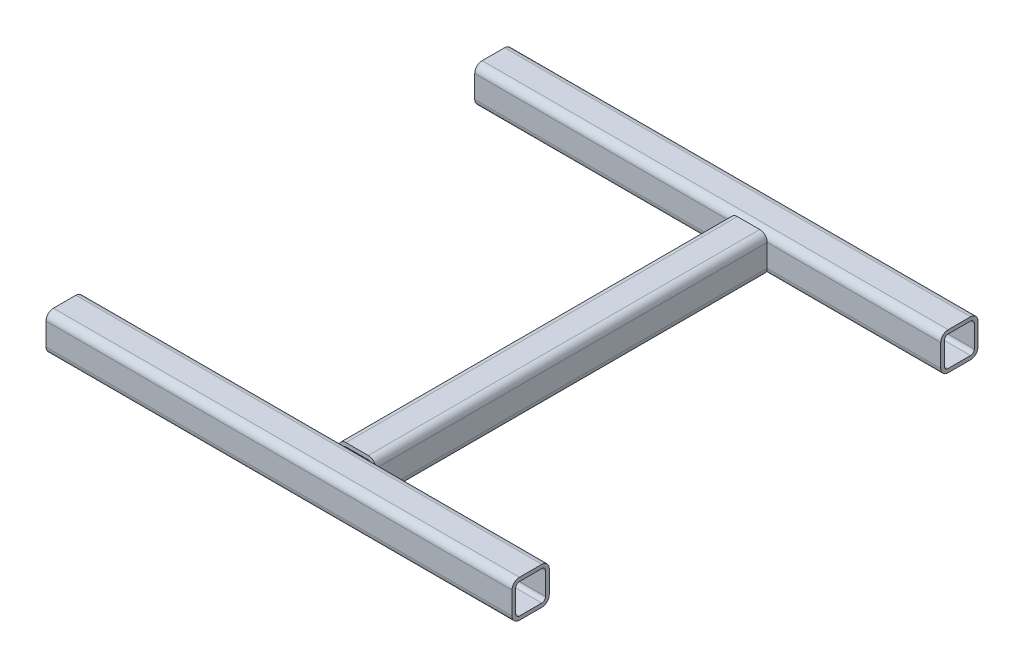
SolidWorks part; units mm, degrees
ref_plane "Front Plane" through (0, 0, 0) normal (0, 0, 1) x (1, 0, 0)
ref_plane "Top Plane" through (0, 0, 0) normal (0, 1, 0) x (1, 0, 0)
ref_plane "Right Plane" through (0, 0, 0) normal (1, 0, 0) x (0, 0, -1)
sketch3d "3DSketch2"
  line L0 (293.8199, 0, 460) -> (293.8199, 0, 0)
  line L1 (0, 0, 0) -> (0, 0, 460) construction
  line L2 (0, 0, 0) -> (500, 0, 0)
  line L3 (500, 0, 0) -> (500, 0, 460) construction
  line L4 (0, 0, 460) -> (500, 0, 460)
  dimension "D1" = 460
  dimension "D2" = 500
  dimension "D3" = 460
other "Square tube 40 X 40 X 4(1)"
ref_plane "Plane1" through (0, 0, 0) normal (1, 0, 0) x (0, 0, -1)
sketch "Sketch1" plane through (0, 0, 0) normal (1, 0, 0) x (0, 0, -1)
  line L0 (-12, -16) -> (12, -16)
  line L1 (-16, -12) -> (-16, 12)
  line L2 (12, 16) -> (-12, 16)
  line L3 (16, 12) -> (16, -12)
  line L4 (-12, -20) -> (12, -20)
  line L5 (-20, -12) -> (-20, 12)
  line L6 (12, 20) -> (-12, 20)
  line L7 (20, 12) -> (20, -12)
  arc A0 (20, 12) -> (12, 20) centre (12, 12) ccw
  arc A1 (12, -20) -> (20, -12) centre (12, -12) ccw
  arc A2 (-20, -12) -> (-12, -20) centre (-12, -12) ccw
  arc A3 (-12, 20) -> (-20, 12) centre (-12, 12) ccw
  arc A4 (-12, 16) -> (-16, 12) centre (-12, 12) ccw
  arc A5 (16, 12) -> (12, 16) centre (12, 12) ccw
  arc A6 (12, -16) -> (16, -12) centre (12, -12) ccw
  arc A7 (-16, -12) -> (-12, -16) centre (-12, -12) ccw
  point P0 (-20, 0)
  point P1 (20, 0)
  point P2 (0, 20)
  point P3 (0, -20)
  point P4 (0, 0)
  point P5 (-20, -20)
  point P6 (20, -20)
  point P7 (20, 20)
  point P8 (-20, 20)
  point P33 (0, 0)
  dimension "D1" = 8
  dimension "Thickness" = 4
  dimension "V_leg" = 40
